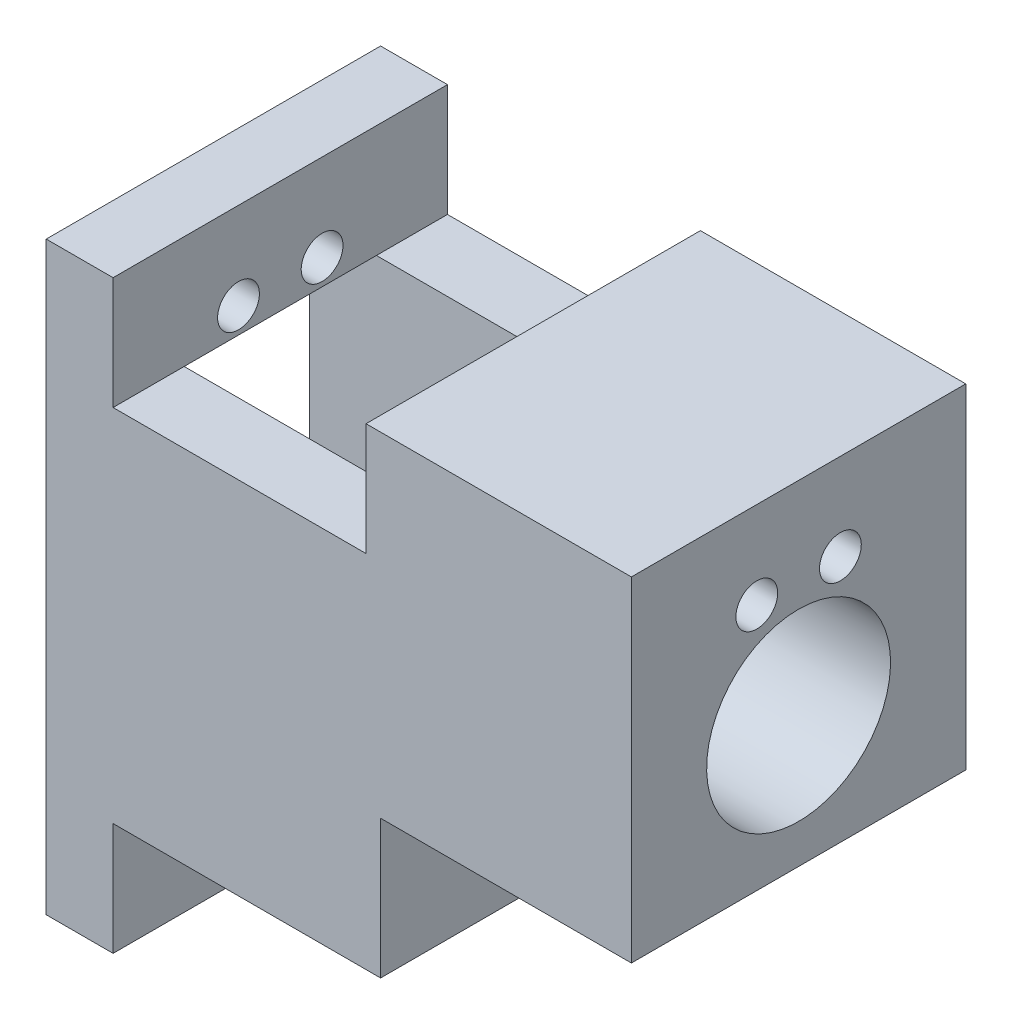
SolidWorks part; units mm, degrees
ref_plane "Front Plane" through (0, 0, 0) normal (0, 0, 1) x (1, 0, 0)
ref_plane "Top Plane" through (0, 0, 0) normal (0, 1, 0) x (1, 0, 0)
ref_plane "Right Plane" through (0, 0, 0) normal (1, 0, 0) x (0, 0, -1)
sketch "Sketch1" plane through (0, 0, 0) normal (0, 0, 1) x (1, 0, 0)
  line L0 (0, 0) -> (-70, 0)
  line L1 (-70, 0) -> (-70, -70)
  line L2 (-70, -70) -> (-30, -70)
  line L3 (-30, -70) -> (-30, -40)
  line L4 (-30, -40) -> (0, -40)
  line L5 (0, -40) -> (0, 0)
  dimension "D1" = 70
  dimension "D2" = 40
  dimension "D3" = 30
  dimension "D4" = 30
extrude "Boss-Extrude1" add sketch "Sketch1" along normal blind 40
sketch "Sketch3" plane through (-70, 0, 0) normal (-1, 0, 0) x (0, 0, 1)
  line L0 (0, -70) -> (20, -70)
  line L1 (40, -70) -> (0, -70) construction
  line L2 (20, -70) -> (8.5, -70)
  line L3 (20, -70) -> (31.5, -70)
  line L4 (0, -70) -> (0, -63)
  line L5 (0, 0) -> (0, -70) construction
  line L6 (8.5, -70) -> (8.5, -7.9)
  line L8 (8.5, -63) -> (31.5, -63)
  line L9 (31.5, -63) -> (31.5, -7.9)
  line L10 (0, -63) -> (0, -7.9)
  line L12 (8.5, -7.9) -> (31.5, -7.9)
  line L14 (0, -35.45) -> (0, -13.45)
  line L15 (0, -35.45) -> (0, -57.45)
  line L16 (8.5, -13.45) -> (31.5, -13.45)
  line L17 (8.5, -57.45) -> (31.5, -57.45)
  line L18 (0, -35.45) -> (0, -10.4)
  line L19 (0, -35.45) -> (0, -60.5)
  line L26 (0, 0) -> (0, -13.45)
  line L29 (20, -57.45) -> (20, -13.45)
  circle A0 centre (15, -60.5) radius 2.5
  circle A1 centre (25, -60.5) radius 2.5
  circle A2 centre (15, -10.4) radius 2.5
  circle A3 centre (25, -10.4) radius 2.5
  dimension "D11" = 5
  dimension "D12" = 5
  dimension "D15" = 5
  dimension "D16" = 5
  dimension "D1" = 11.5
  dimension "D2" = 11.5
  dimension "D3" = 7
  dimension "D4" = 55.1
  dimension "D5" = 22
  dimension "D6" = 22
  dimension "D7" = 25.05
  dimension "D8" = 25.05
  dimension "D17" = 13.45
extrude "Cut-Extrude1" cut sketch "Sketch3" against normal blind 30
sketch "Sketch4" plane through (0, 0, 0) normal (0, 1, 0) x (1, 0, 0)
  line L0 (-70, -20) -> (-70, -31.5)
  line L1 (-70, -40) -> (-70, 0) construction
  line L2 (-70, -31.5) -> (-70, -8.5)
  line L3 (-70, 0) -> (-62, 0)
  line L4 (0, 0) -> (-70, 0) construction
  line L5 (-62, 0) -> (-62, -40)
  line L6 (0, -40) -> (-70, -40) construction
  line L7 (-62, -40) -> (-31.7452, -40)
  line L8 (-31.7452, -40) -> (-31.7452, 0)
  line L9 (-31.7452, 0) -> (-62, 0)
  line M4 (0, 0) -> (-70, 0)
  line M6 (-70, -40) -> (0, -40)
  dimension "D1" = 11.5
  dimension "D2" = 23
  dimension "D3" = 8
extrude "Cut-Extrude2" cut sketch "Sketch4" against normal blind 13.45 contours L8 L5 M6 M4
sketch "Sketch5" plane through (0, -70, 0) normal (0, -1, 0) x (1, 0, 0)
  line L0 (-70, 40) -> (-62, 40)
  line L1 (-70, 40) -> (-30, 40) construction
  line L2 (-62, 40) -> (-62, 0)
  line L3 (-70, 0) -> (-30, 0) construction
  line L4 (-62, 0) -> (-30, 0)
  line L5 (-30, 0) -> (-30, 40)
  line L6 (-30, 40) -> (-62, 40)
  line M1 (-70, 0) -> (-30, 0)
  line M2 (-30, 0) -> (-30, 40)
  line M3 (-30, 40) -> (-70, 40)
  dimension "D1" = 8
extrude "Cut-Extrude3" cut sketch "Sketch5" against normal blind 13.45 contours L2 M3 M1 M2
sketch "Sketch6" plane through (-70, 0, 0) normal (-1, 0, 0) x (0, 0, 1)
  line L0 (20, -13.45) -> (20, -10.4)
  line L1 (8.5, -13.45) -> (31.5, -13.45) construction
  line L2 (20, -10.4) -> (25, -10.4)
  line L3 (25, -10.4) -> (15, -10.4)
  line L4 (20, -57.45) -> (20, -60.5)
  line L5 (8.5, -57.45) -> (31.5, -57.45) construction
  line L6 (20, -60.5) -> (25, -60.5)
  line L7 (25, -60.5) -> (15, -60.5)
  circle A0 centre (15, -10.4) radius 2.5
  circle A1 centre (25, -10.4) radius 2.5
  circle A2 centre (25, -60.5) radius 2.5
  circle A3 centre (15, -60.5) radius 2.5
  dimension "D6" = 5
  dimension "D7" = 5
  dimension "D8" = 5
  dimension "D9" = 5
  dimension "D1" = 3.05
  dimension "D2" = 5
  dimension "D3" = 10
  dimension "D4" = 3.05
  dimension "D5" = 10
extrude "Cut-Extrude4" cut sketch "Sketch6" against normal blind 100
sketch "Sketch7" plane through (0, 0, 0) normal (1, 0, 0) x (0, 0, -1)
  line L0 (0, -40) -> (0, -24.34)
  line L1 (0, -40) -> (0, 0) construction
  line L2 (0, -24.34) -> (-40, -24.34)
  line L3 (-40, -40) -> (-40, 0) construction
  circle A0 centre (-20, -24.34) radius 11
  dimension "D2" = 22
  dimension "D1" = 15.66
extrude "Cut-Extrude5" cut sketch "Sketch7" against normal blind 28.12 contours L2 A0 | L2 A0
